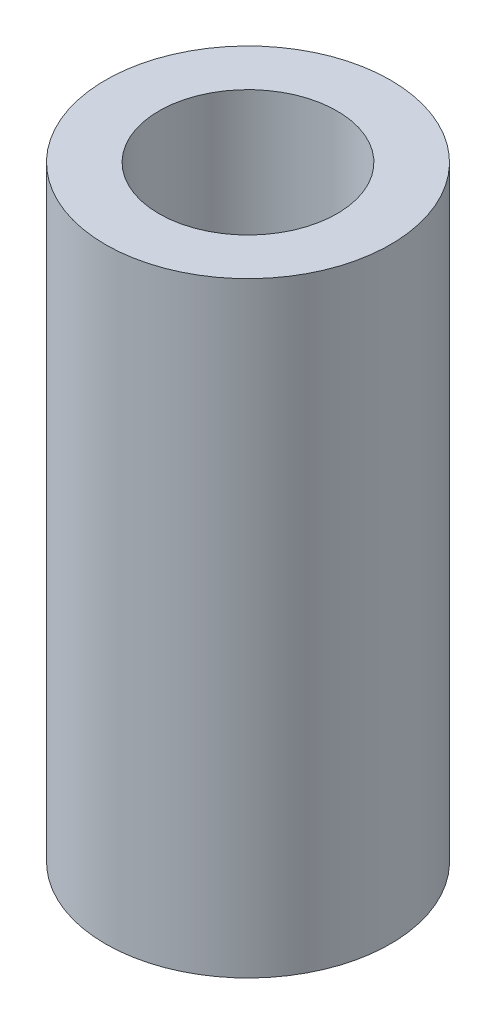
SolidWorks part; units mm, degrees
ref_plane "Front Plane" through (0, 0, 0) normal (0, 0, 1) x (1, 0, 0)
ref_plane "Top Plane" through (0, 0, 0) normal (0, 1, 0) x (1, 0, 0)
ref_plane "Right Plane" through (0, 0, 0) normal (1, 0, 0) x (0, 0, -1)
sketch "Sketch2" plane through (0, 0, 0) normal (0, 1, 0) x (1, 0, 0)
  circle A0 centre (0, 0) radius 4
  circle A1 centre (0, 0) radius 2.5
extrude "Boss-Extrude1" add sketch "Sketch2" along normal blind 17 contours A0 | A1
